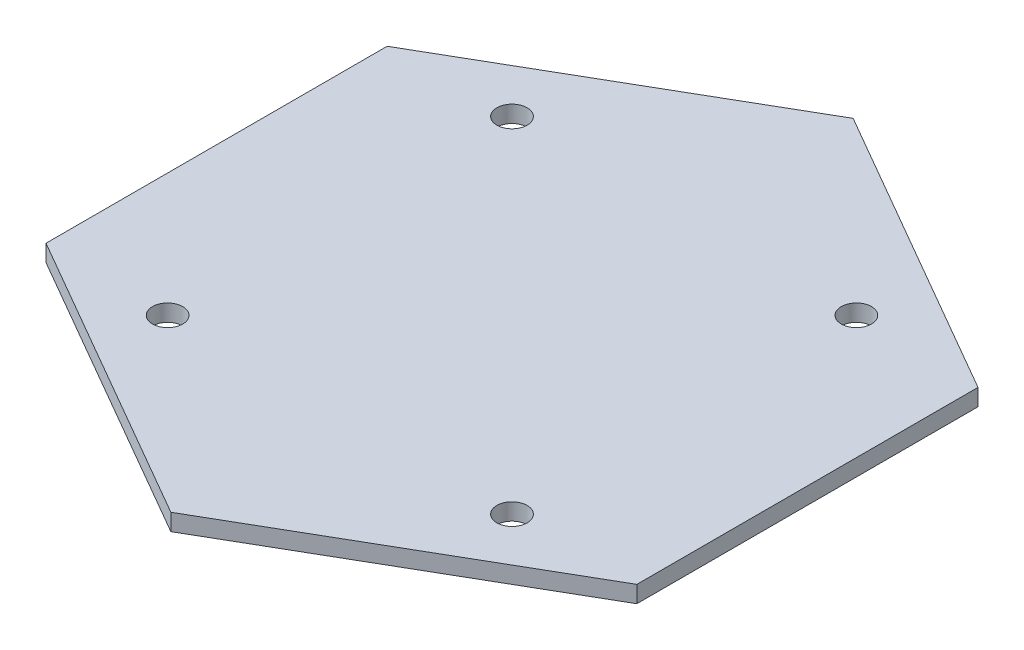
SolidWorks part; units mm, degrees
ref_plane "Front Plane" through (0, 0, 0) normal (0, 0, 1) x (1, 0, 0)
ref_plane "Top Plane" through (0, 0, 0) normal (0, 1, 0) x (1, 0, 0)
ref_plane "Right Plane" through (0, 0, 0) normal (1, 0, 0) x (0, 0, -1)
sketch "Sketch1" plane through (0, 0, 0) normal (0, 1, 0) x (1, 0, 0)
  line L0 (0, 0) -> (18.6185, 0)
  line L1 (0, 0) -> (0, 56.6281)
  line L2 (0, 0) -> (0, -18.6185)
  line L3 (0, 0) -> (56.6281, 0)
  line L4 (0, 0) -> (-18.6185, 0)
  line L5 (0, 0) -> (0, -56.6281)
  line L6 (0, 0) -> (0, 18.6185)
  line L7 (0, 0) -> (-56.6281, 0)
  line L14 (0, 51.5792) -> (-44.6689, 25.7896)
  line L15 (-44.6689, 25.7896) -> (-44.6689, -25.7896)
  line L16 (-44.6689, -25.7896) -> (0, -51.5792)
  line L17 (0, -51.5792) -> (44.6689, -25.7896)
  line L18 (44.6689, -25.7896) -> (44.6689, 25.7896)
  line L19 (44.6689, 25.7896) -> (0, 51.5792)
  circle A0 centre (-26.035, 26.035) radius 2.286
  circle A1 centre (26.035, 26.035) radius 2.286
  circle A2 centre (26.035, -26.035) radius 2.286
  circle A3 centre (-26.035, -26.035) radius 2.286
  circle A5 centre (0, 0) radius 44.6689 construction
  point P21 (0, 0)
  dimension "D3" = 4.572
  dimension "D1" = 26.035
  dimension "D2" = 26.035
  dimension "D4" = 4
extrude "Boss-Extrude1" add sketch "Sketch1" along normal blind 2.54
sketch "Sketch2" plane through (0, 0, 0) normal (0, -1, 0) x (1, 0, 0)
  circle A0 centre (0, 0) radius 9.906
  circle A1 centre (0, 0) radius 11.684
  dimension "D1" = 19.812
  dimension "D2" = 23.368
extrude "Boss-Extrude2" add sketch "Sketch2" along normal blind 15.875
fillet "Fillet1" radius 3.175 1 edges at (0, 0, 11.684)
sketch "Sketch4" plane through (0, 0, 0) normal (0, 0, 1) x (1, 0, 0)
  line L1 (-9.906, -1.524) -> (-8.128, -1.4224)
  line L2 (-9.906, 0) -> (9.906, 0) construction
  line L3 (0, 0) -> (-44.6689, 0) construction
  line L4 (-9.906, 0) -> (-9.906, -1.524)
  line L6 (0, 0) -> (0, -39.677) construction
  line L7 (-8.128, -1.4224) -> (-8.128, -0.1016)
  line L8 (-9.906, 0) -> (-8.128, -0.1016)
  dimension "D1" = 1.524
sketch "Sketch6" plane through (0, 0, 0) normal (0, -1, 0) x (1, 0, 0)
  circle A0 centre (0, 0) radius 9.906
curve "Helix/Spiral1" pitch 5.08 height 14.224 turns 2.8
sweep "Sweep2" add profiles "Sketch4" path "Helix/Spiral1"
